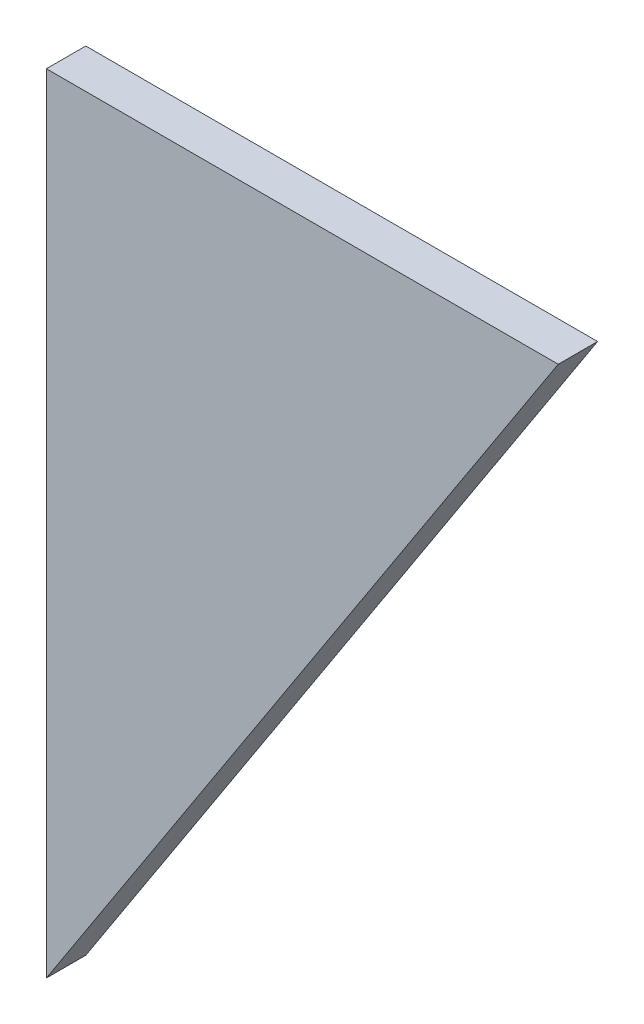
SolidWorks part; units mm, degrees
ref_plane "Alzado" through (0, 0, 0) normal (0, 0, 1) x (1, 0, 0)
ref_plane "Planta" through (0, 0, 0) normal (0, 1, 0) x (1, 0, 0)
ref_plane "Vista lateral" through (0, 0, 0) normal (1, 0, 0) x (0, 0, -1)
sketch "Sketch1" plane through (0, 0, 0) normal (0, 0, 1) x (1, 0, 0)
  line L0 (65, 100) -> (-65, 100)
  line L5 (-65, -100) -> (65, 100) construction
  line L6 (-65, -100) -> (65, 100)
  line L7 (-65, -100) -> (-65, 100)
  point P0 (0, 0)
  dimension "D1" = 200
  dimension "D2" = 130
extrude "Boss-Extrude1" add sketch "Sketch1" along normal blind 10
